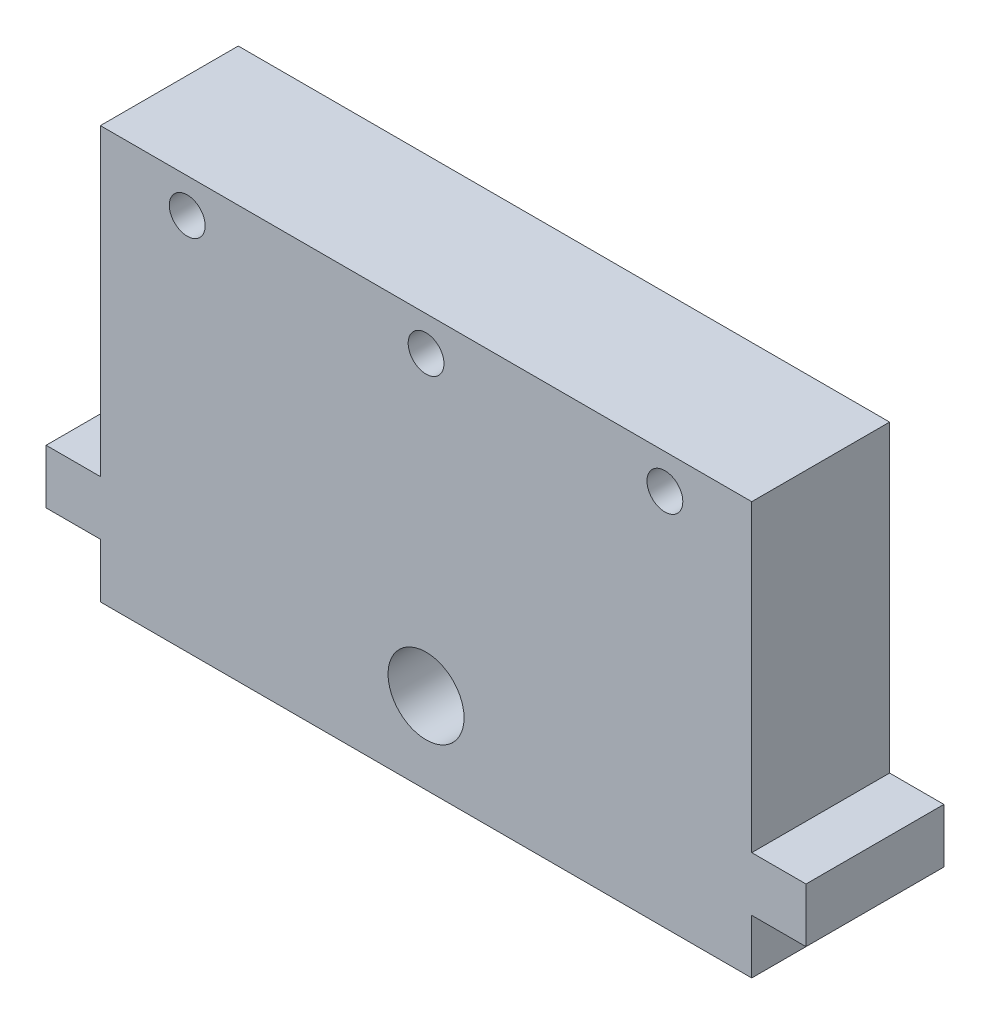
SolidWorks part; units mm, degrees
ref_plane "Front Plane" through (0, 0, 0) normal (0, 0, 1) x (1, 0, 0)
ref_plane "Top Plane" through (0, 0, 0) normal (0, 1, 0) x (1, 0, 0)
ref_plane "Right Plane" through (0, 0, 0) normal (1, 0, 0) x (0, 0, -1)
sketch "Sketch1" plane through (0, 0, 0) normal (0, 1, 0) x (1, 0, 0)
  line L1 (0, 0) -> (-60, 0)
  line L2 (0, 0) -> (0, 12.7)
  line L3 (0, 12.7) -> (-60, 12.7)
  line L4 (-60, 0) -> (-60, 12.7)
  dimension "D1" = 12.7
  dimension "D2" = 60
extrude "Boss-Extrude1" add sketch "Sketch1" along normal blind 38
sketch "Sketch2" plane through (0, 0, 0) normal (0, 0, 1) x (1, 0, 0)
  line L0 (-30, 0) -> (-30, 38) construction
  line L1 (-60, 0) -> (0, 0) construction
  line L2 (-60, 38) -> (0, 38) construction
  line L3 (-60, 22.5) -> (0, 22.5) construction
  line L4 (-60, 38) -> (-60, 0) construction
  line L5 (0, 38) -> (0, 0) construction
  point P12 (-30, 7.5)
  point P13 (-54, 22.5)
  point P14 (-6, 22.5)
  dimension "D1" = 7.5
  dimension "D2" = 15
  dimension "D3" = 24
hole_wizard "M5x0.8 Tapped Hole1" [suppressed] positions "3DSketch1" profile "Sketch3" tap size "M5x0.8" standard "ANSI Metric"
sketch3d "3DSketch1"
  point P0 (-54, 22.5, 0)
  point P3 (-6, 22.5, 0)
cosmetic thread "Hole Thread1" [suppressed] parameters "D2"=5
cosmetic thread "Hole Thread2" [suppressed] parameters "D2"=5
sketch "Sketch3" plane through (-54, 22.5, 0) normal (1, 0, 0) x (0, -1, 0)
  line L0 (0, 0) -> (0, 12.7)
  line L1 (0, 12.7) -> (2.1, 12.7)
  line L2 (2.1, 12.7) -> (2.1, 0)
  line L5 (2.1, 0) -> (0, 0)
  line L11 (0, -6.35) -> (0, 107.95) construction
  dimension "Thru Tap Drill Dia." = 4.2
  dimension "Thru Tap Drill Depth" = 12.7
hole_wizard "M8x1.0 Tapped Hole1" positions "3DSketch2" profile "Sketch4" tap size "M8x1.0" standard "ANSI Metric"
sketch3d "3DSketch2"
  point P0 (-30, 7.5, 0)
sketch "Sketch4" plane through (-30, 7.5, 0) normal (1, 0, 0) x (0, -1, 0)
  line L0 (0, 0) -> (0, 21.153)
  line L1 (0, 21.153) -> (3.5, 19.05)
  line L2 (3.5, 19.05) -> (3.5, 0)
  line L5 (3.5, 0) -> (0, 0)
  line L10 (0, 21.153) -> (-3.5, 19.05) construction
  line L11 (0, -6.35) -> (0, 107.95) construction
  dimension "Tap Drill Dia." = 7
  dimension "Tap Drill Depth" = 19.05
  dimension "Drill Angle" = 118
cosmetic thread "Hole Thread3" parameters "D1"=12.7, "D2"=8
sketch "Sketch5" plane through (0, 0, -12.7) normal (0, 0, -1) x (-1, 0, 0)
  line L0 (30, 0) -> (30, 38) construction
  line L1 (0, 0) -> (10, 0)
  line L2 (0, 0) -> (0, 15)
  line L3 (0, 15) -> (10, 15)
  line L4 (10, 0) -> (10, 15)
  line L5 (60, 15) -> (50, 15)
  line L6 (50, 0) -> (50, 15)
  line L7 (60, 0) -> (50, 0)
  line L8 (60, 0) -> (60, 15)
  dimension "D1" = 15
  dimension "D2" = 10
extrude "Boss-Extrude2" [suppressed] add sketch "Sketch5" along normal blind 10
sketch "Sketch6" [suppressed] plane through (0, 0, 0) normal (1, 0, 0) x (0, 0, -1)
  line L0 (22.7, 7.5) -> (0, 7.5) construction
  line L1 (22.7, 15) -> (22.7, 0) construction
  line L2 (0, 0) -> (0, 30) construction
  line L3 (0, 0) -> (22.7, 0) construction
  line L4 (17.7, 15) -> (17.7, 0) construction
  line L5 (22.7, 15) -> (12.7, 15) construction
  point P12 (17.7, 7.5)
  dimension "D1" = 7.5
sketch "Sketch7" plane through (0, 0, 0) normal (0, 0, 1) x (1, 0, 0)
  line L0 (-30, 7.5) -> (-60, 7.5) construction
  line L1 (-60, 38) -> (-60, 0) construction
  line L2 (-60, 7.5) -> (-60, 10)
  line L3 (-60, 10) -> (-65, 10)
  line L4 (-65, 10) -> (-65, 5)
  line L5 (-65, 5) -> (-60, 5)
  line L6 (-60, 5) -> (-60, 7.5)
  line L7 (-30, 0) -> (-30, 7.5) construction
  line L8 (5, 5) -> (0, 5)
  line L9 (5, 10) -> (5, 5)
  line L10 (0, 10) -> (5, 10)
  line L11 (0, 7.5) -> (0, 10)
  line L12 (0, 5) -> (0, 7.5)
  dimension "D1" = 2.5
  dimension "D2" = 5
  dimension "D3" = 5
extrude "Boss-Extrude3" add sketch "Sketch7" against normal up to vertex (12.7 mm away)
sketch "Sketch8" plane through (0, 0, 0) normal (0, 0, 1) x (1, 0, 0)
  line L0 (0, 38) -> (0, 10) construction
  line L1 (-60, 38) -> (0, 38)
  line L2 (-60, 38) -> (-60, 31.65)
  line L3 (-60, 31.65) -> (0, 31.65)
  line L4 (0, 38) -> (0, 31.65)
  line L5 (-60, 34.825) -> (0, 34.825) construction
  line L6 (-30, 0) -> (-30, 38) construction
  point P9 (-30, 34.825)
  point P10 (-8, 34.825)
  point P11 (-52, 34.825)
  dimension "D1" = 6.35
  dimension "D2" = 22
  dimension "D3" = 22
hole_wizard "M4x0.7 Tapped Hole1" positions "3DSketch3" profile "Sketch10" tap size "M4x0.7" standard "ANSI Metric" end condition through all
sketch3d "3DSketch3"
  point P0 (-52, 34.825, 0)
  point P3 (-30, 34.825, 0)
  point P6 (-8, 34.825, 0)
sketch "Sketch10" plane through (-52, 34.825, 0) normal (1, 0, 0) x (0, -1, 0)
  line L0 (0, 0) -> (0, 12.7)
  line L1 (0, 12.7) -> (1.65, 12.7)
  line L2 (1.65, 12.7) -> (1.65, 0)
  line L5 (1.65, 0) -> (0, 0)
  line L11 (0, -6.35) -> (0, 107.95) construction
  dimension "Thru Tap Drill Dia." = 3.3
  dimension "Thru Tap Drill Depth" = 12.7
cosmetic thread "Hole Thread4" parameters "D2"=4
cosmetic thread "Hole Thread5" parameters "D2"=4
cosmetic thread "Hole Thread6" parameters "D2"=4
